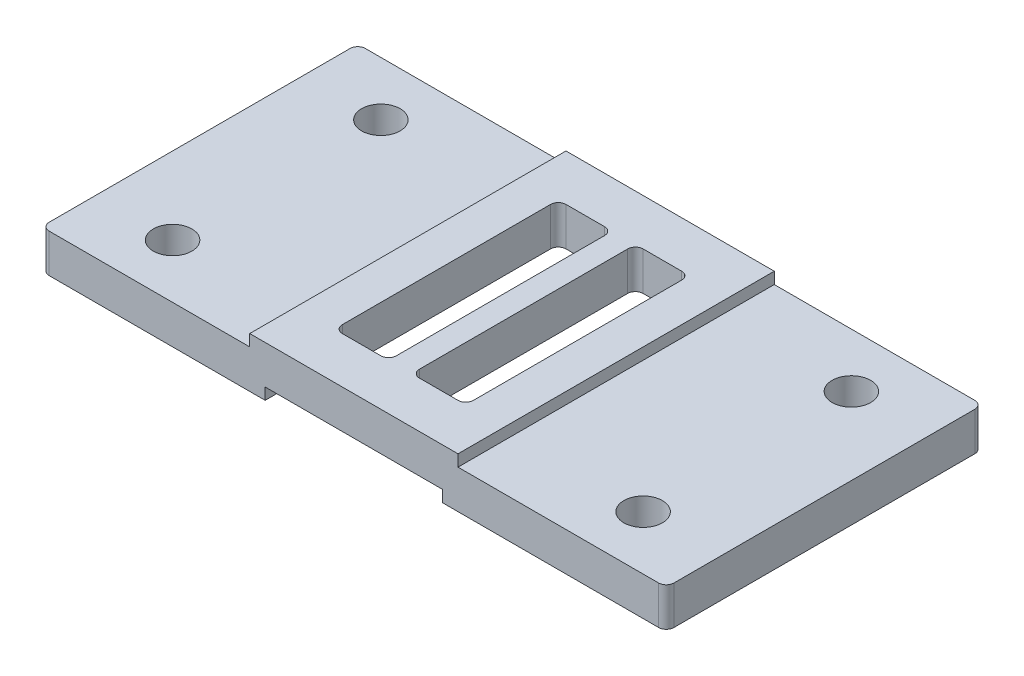
SolidWorks part; units mm, degrees
ref_plane "Front Plane" through (0, 0, 0) normal (0, 0, 1) x (1, 0, 0)
ref_plane "Top Plane" through (0, 0, 0) normal (0, 1, 0) x (1, 0, 0)
ref_plane "Right Plane" through (0, 0, 0) normal (1, 0, 0) x (0, 0, -1)
ref_plane "Plane1" through (0, 8, 0) normal (0, 1, 0) x (1, 0, 0)
sketch "Sketch1" plane through (0, 8, 0) normal (0, 1, 0) x (1, 0, 0)
  line L0 (81, 41) -> (-81, 41)
  line L1 (-81, 41) -> (-81, -41)
  line L2 (-81, -41) -> (81, -41)
  line L3 (81, -41) -> (81, 41)
extrude "Boss-Extrude1" add sketch "Sketch1" against normal blind 13
sketch "Sketch2" plane through (0, 0, -41) normal (0, 0, -1) x (-1, 0, 0)
  line L0 (-81, 5) -> (-27, 5)
  line L1 (-27, 5) -> (-27, 8)
  line L2 (-27, 8) -> (-81, 8)
  line L3 (-81, 8) -> (-81, 5)
extrude "Cut-Extrude1" cut sketch "Sketch2" against normal through all
sketch "Sketch3" plane through (0, 0, -41) normal (0, 0, -1) x (-1, 0, 0)
  line L0 (27, 8) -> (27, 5)
  line L1 (27, 5) -> (81, 5)
  line L2 (81, 5) -> (81, 8)
  line L3 (81, 8) -> (27, 8)
extrude "Cut-Extrude2" cut sketch "Sketch3" against normal through all
sketch "Sketch4" plane through (0, 0, -41) normal (0, 0, -1) x (-1, 0, 0)
  line L0 (-23, -5) -> (23, -5)
  line L1 (23, -5) -> (23, -2)
  line L2 (23, -2) -> (-23, -2)
  line L3 (-23, -2) -> (-23, -5)
extrude "Cut-Extrude3" cut sketch "Sketch4" against normal through all
sketch "Sketch5" plane through (0, -2, 0) normal (0, -1, 0) x (1, 0, 0)
  line L0 (-3, 29) -> (-17, 29)
  line L1 (-17, 29) -> (-17, -29)
  line L2 (-17, -29) -> (-3, -29)
  line L3 (-3, -29) -> (-3, 29)
extrude "Cut-Extrude4" cut sketch "Sketch5" against normal through all
sketch "Sketch6" plane through (0, 8, 0) normal (0, 1, 0) x (-1, 0, 0)
  line L0 (-3, -29) -> (-3, 29)
  line L1 (-3, 29) -> (-17, 29)
  line L2 (-17, 29) -> (-17, -29)
  line L3 (-17, -29) -> (-3, -29)
extrude "Cut-Extrude5" cut sketch "Sketch6" against normal through all
hole_wizard "3/8 Clearance Hole1" positions "Sketch8" profile "Sketch7" hole size "3/8" standard "ANSI Inch"
sketch "Sketch8" plane through (0, 5, 0) normal (0, 1, 0) x (1, 0, 0)
  point P0 (-61, 27)
  point P1 (61, 27)
  point P2 (-61, -27)
  point P3 (61, -27)
sketch "Sketch7" plane through (-61, 5, -27) normal (1, 0, 0) x (0, 0, 1)
  line L0 (0, 0) -> (0, 10)
  line L1 (0, 10) -> (5, 10)
  line L2 (5, 10) -> (5, 0)
  line L5 (5, 0) -> (0, 0)
  line L11 (0, -6.35) -> (0, 107.95) construction
  dimension "Thru Hole Dia." = 10
  dimension "Thru Hole Depth" = 10
fillet "Fillet1" radius 2 12 edges at (-3, 3, -29) (3, 3, -29) (17, 3, 29) (81, 0, 41) (-17, 3, -29) (-81, 0, -41) (3, 3, 29) (-81, 0, 41) (17, 3, -29) (-3, 3, 29) (81, 0, -41) (-17, 3, 29)
